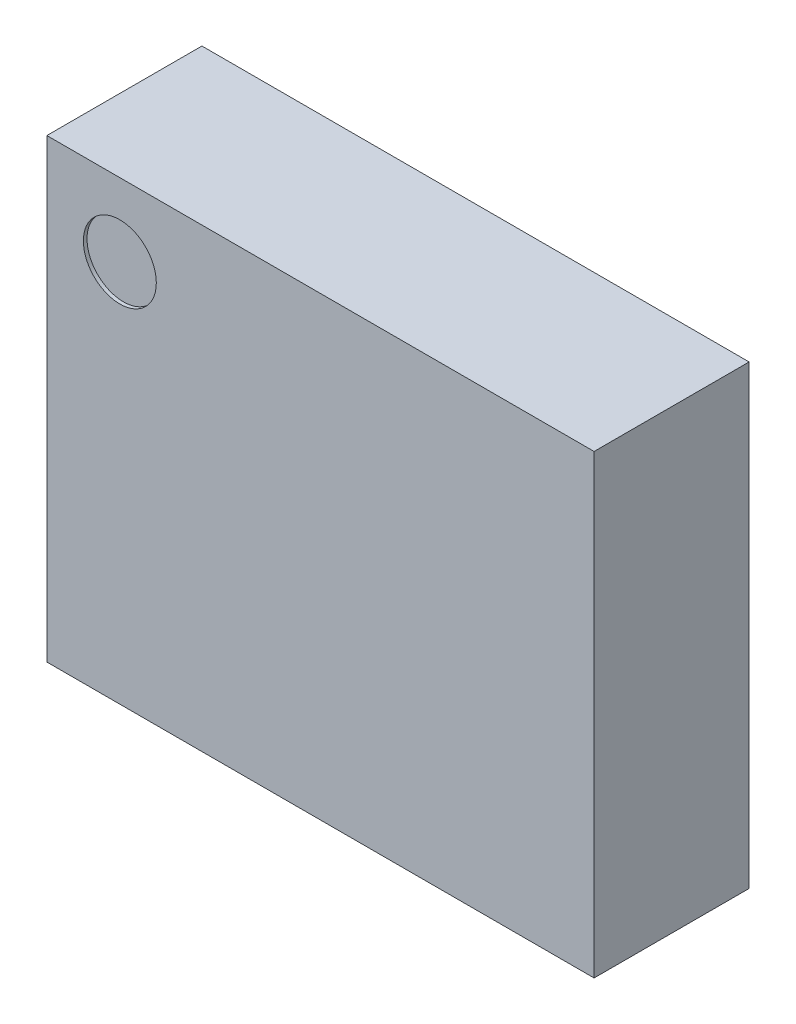
SolidWorks part; units mm, degrees
ref_plane "Front Plane" through (0, 0, 0) normal (0, 0, 1) x (1, 0, 0)
ref_plane "Top Plane" through (0, 0, 0) normal (0, 1, 0) x (1, 0, 0)
ref_plane "Right Plane" through (0, 0, 0) normal (1, 0, 0) x (0, 0, -1)
sketch "Sketch1" plane through (0, 0, 0) normal (0, 0, 1) x (1, 0, 0)
  line L1 (-1.5, 1.25) -> (1.5, 1.25)
  line L2 (-1.5, 1.25) -> (-1.5, -1.25)
  line L3 (-1.5, -1.25) -> (1.5, -1.25)
  line L4 (1.5, 1.25) -> (1.5, -1.25)
  line L5 (-1.5, 1.25) -> (1.5, -1.25) construction
  line L6 (-1.5, -1.25) -> (1.5, 1.25) construction
  point P0 (0, 0)
  dimension "D1" = 3
  dimension "D2" = 2.5
extrude "Boss-Extrude1" add sketch "Sketch1" along normal blind 0.8
sketch "Sketch2" plane through (0, 0, 0.8) normal (0, 0, 1) x (1, 0, 0)
  line L0 (-1.5, 1.25) -> (1, -1.25) construction
  line L1 (-1.5, -1.25) -> (1.5, -1.25) construction
  line L2 (1.5, 1.25) -> (-1.5, 1.25) construction
  circle A0 centre (-1.1, 0.85) radius 0.2
  dimension "D3" = 0.4
  dimension "D1" = 45
  dimension "D2" = 0.4
extrude "Cut-Extrude1" cut sketch "Sketch2" against normal blind 0.02
sketch "Sketch3" plane through (0, 0, 0) normal (0, 0, -1) x (-1, 0, 0)
  line L0 (0, 1.25) -> (0, -1.25) construction
  line L1 (-1.5, 1.25) -> (1.5, 1.25) construction
  line L2 (1.5, -1.25) -> (-1.5, -1.25) construction
  line L3 (0.375, 1.15) -> (0.375, 0.675)
  line L4 (-0.125, 1.15) -> (0.125, 1.15)
  line L5 (-0.125, 1.15) -> (-0.125, 0.675)
  line L6 (-0.125, 0.675) -> (0.125, 0.675)
  line L7 (0.125, 1.15) -> (0.125, 0.675)
  line L8 (-0.125, 1.15) -> (0.125, 0.675) construction
  line L9 (-0.125, 0.675) -> (0.125, 1.15) construction
  line L10 (0.375, 1.15) -> (0.625, 1.15)
  line L11 (0.625, 1.15) -> (0.625, 0.675)
  line L12 (0.375, 0.675) -> (0.625, 0.675)
  line L13 (-0.375, 1.15) -> (-0.625, 1.15)
  line L14 (-0.625, 1.15) -> (-0.625, 0.675)
  line L15 (-0.375, 0.675) -> (-0.625, 0.675)
  line L16 (-0.375, 1.15) -> (-0.375, 0.675)
  line L17 (-1.5, 0) -> (1.5, 0) construction
  line L18 (-1.5, -1.25) -> (-1.5, 1.25) construction
  line L19 (1.5, 1.25) -> (1.5, -1.25) construction
  line L20 (0.375, -1.15) -> (0.625, -1.15)
  line L21 (0.625, -1.15) -> (0.625, -0.675)
  line L22 (0.375, -0.675) -> (0.625, -0.675)
  line L23 (0.375, -1.15) -> (0.375, -0.675)
  line L24 (-0.125, -0.675) -> (0.125, -0.675)
  line L25 (0.125, -1.15) -> (0.125, -0.675)
  line L26 (-0.125, -1.15) -> (0.125, -1.15)
  line L27 (-0.125, -1.15) -> (-0.125, -0.675)
  line L28 (-0.375, -1.15) -> (-0.375, -0.675)
  line L29 (-0.375, -0.675) -> (-0.625, -0.675)
  line L30 (-0.625, -1.15) -> (-0.625, -0.675)
  line L31 (-0.375, -1.15) -> (-0.625, -1.15)
  line L32 (-1.4, -0.125) -> (-0.925, -0.125)
  line L33 (-1.4, 0.375) -> (-0.925, 0.375)
  line L34 (-1.4, 0.375) -> (-1.4, 0.125)
  line L35 (-1.4, 0.125) -> (-0.925, 0.125)
  line L36 (-0.925, 0.375) -> (-0.925, 0.125)
  line L37 (-1.4, 0.375) -> (-0.925, 0.125) construction
  line L38 (-1.4, 0.125) -> (-0.925, 0.375) construction
  line L39 (-0.925, -0.375) -> (-0.925, -0.125)
  line L40 (-1.4, -0.375) -> (-0.925, -0.375)
  line L41 (-1.4, -0.375) -> (-1.4, -0.125)
  line L42 (-1.4, -0.125) -> (-0.925, -0.375) construction
  line L43 (-1.4, -0.625) -> (-0.925, -0.625)
  line L44 (-1.4, 0.875) -> (-0.925, 0.875)
  line L45 (-1.4, 0.875) -> (-1.4, 0.625)
  line L46 (-1.4, 0.625) -> (-0.925, 0.625)
  line L47 (-0.925, 0.875) -> (-0.925, 0.625)
  line L48 (-1.4, 0.875) -> (-0.925, 0.625) construction
  line L49 (-1.4, 0.625) -> (-0.925, 0.875) construction
  line L50 (-0.925, -0.875) -> (-0.925, -0.625)
  line L51 (-1.4, -0.875) -> (-0.925, -0.875)
  line L52 (-1.4, -0.875) -> (-1.4, -0.625)
  line L53 (1.4, -0.875) -> (1.4, -0.625)
  line L54 (1.4, -0.875) -> (0.925, -0.875)
  line L55 (0.925, -0.875) -> (0.925, -0.625)
  line L56 (1.4, -0.625) -> (0.925, -0.625)
  line L57 (1.4, -0.375) -> (1.4, -0.125)
  line L58 (1.4, -0.375) -> (0.925, -0.375)
  line L59 (0.925, -0.375) -> (0.925, -0.125)
  line L60 (1.4, -0.125) -> (0.925, -0.125)
  line L61 (1.4, 0.125) -> (0.925, 0.125)
  line L62 (0.925, 0.375) -> (0.925, 0.125)
  line L63 (1.4, 0.375) -> (0.925, 0.375)
  line L64 (1.4, 0.375) -> (1.4, 0.125)
  line L65 (1.4, 0.625) -> (0.925, 0.625)
  line L66 (0.925, 0.875) -> (0.925, 0.625)
  line L67 (1.4, 0.875) -> (0.925, 0.875)
  line L68 (1.4, 0.875) -> (1.4, 0.625)
  point P6 (0, 0.9125)
  point P37 (-1.1625, 0.25)
  point P46 (-1.1625, -0.25)
  point P47 (-1.1625, 0.75)
  point P52 (0, 0)
  dimension "D1" = 0.25
  dimension "D2" = 0.475
  dimension "D3" = 0.1
  dimension "D5" = 0.1
  dimension "D6" = 0.5
  dimension "D7" = 0.5
  dimension "D4" = 2
extrude "Boss-Extrude2" add sketch "Sketch3" along normal blind 0.1
sketch "Sketch4" plane through (0, 0, 0) normal (0, 0, -1) x (-1, 0, 0)
  line L4 (-1.5, 1.25) -> (-1.5, -1.25)
  line L5 (-1.5, -1.25) -> (1.5, -1.25)
  line L6 (1.5, -1.25) -> (1.5, 1.25)
  line L7 (1.5, 1.25) -> (-1.5, 1.25)
  line L8 (-1.5, 1.25) -> (-1.5, -1.25)
  line L9 (-1.5, -1.25) -> (1.5, -1.25)
  line L10 (1.5, -1.25) -> (1.5, 1.25)
  line L11 (1.5, 1.25) -> (-1.5, 1.25)
  dimension "D1" = 0
extrude "Boss-Extrude3" add sketch "Sketch4" along normal blind 0.05
